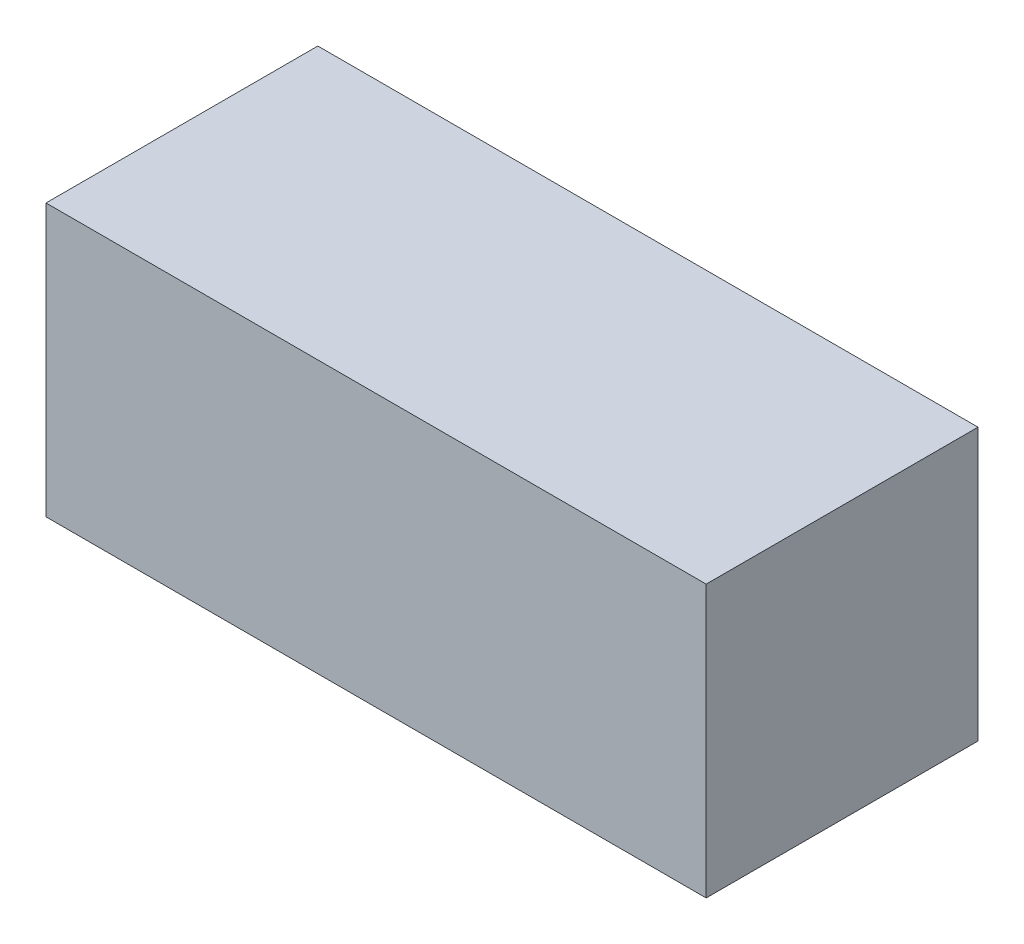
SolidWorks part; units mm, degrees
ref_plane "Front Plane" through (0, 0, 0) normal (0, 0, 1) x (1, 0, 0)
ref_plane "Top Plane" through (0, 0, 0) normal (0, 1, 0) x (1, 0, 0)
ref_plane "Right Plane" through (0, 0, 0) normal (1, 0, 0) x (0, 0, -1)
sketch "Эскиз1" plane through (0, 0, 0) normal (0, 0, 1) x (1, 0, 0)
  line L1 (-85, -35) -> (85, -35)
  line L2 (-85, -35) -> (-85, 35)
  line L3 (-85, 35) -> (85, 35)
  line L4 (85, -35) -> (85, 35)
  line L5 (-85, -35) -> (85, 35) construction
  line L6 (-85, 35) -> (85, -35) construction
  point P0 (0, 0)
  dimension "D1" = 170
  dimension "D2" = 70
extrude "Бобышка-Вытянуть1" add sketch "Эскиз1" along normal mid plane 70
